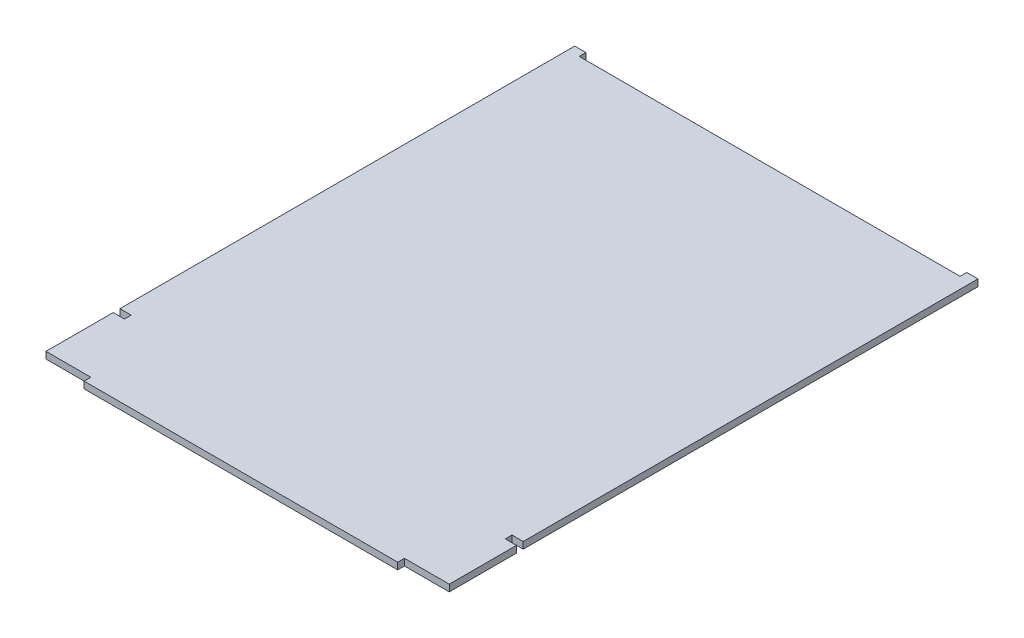
SolidWorks part; units mm, degrees
ref_plane "前视基准面" through (0, 0, 0) normal (0, 0, 1) x (1, 0, 0)
ref_plane "上视基准面" through (0, 0, 0) normal (0, 1, 0) x (1, 0, 0)
ref_plane "右视基准面" through (0, 0, 0) normal (1, 0, 0) x (0, 0, -1)
sketch "草图1" plane through (0, 0, 0) normal (0, 1, 0) x (1, 0, 0)
  line L2 (0, 0) -> (0, 27)
  line L3 (0, 30) -> (5, 30)
  line L4 (180, 0) -> (180, 27)
  line L5 (0, 30) -> (5, 30)
  line L6 (0, 30) -> (0, 230)
  line L7 (5, 230) -> (175, 230)
  line L8 (180, 30) -> (180, 230)
  line L13 (0, 30) -> (5, 30)
  line L14 (5, 30) -> (5, 27)
  line L15 (5, 27) -> (0, 27)
  line L16 (180, 30) -> (175, 30)
  line L17 (175, 30) -> (175, 27)
  line L18 (175, 27) -> (180, 27)
  line L19 (175, 30) -> (180, 30)
  line L20 (175, 30) -> (180, 30)
  line L21 (0, 230) -> (0, 233)
  line L22 (0, 233) -> (5, 233)
  line L23 (5, 233) -> (5, 230)
  line L25 (175, 230) -> (175, 233)
  line L26 (175, 233) -> (180, 233)
  line L27 (180, 233) -> (180, 230)
  line L29 (0, 0) -> (0, -3)
  line L30 (0, -3) -> (20, -3)
  line L31 (20, -3) -> (20, -6)
  line L32 (20, -6) -> (160, -6)
  line L33 (160, -6) -> (160, -3)
  line L34 (160, -3) -> (180, -3)
  line L35 (180, -3) -> (180, 0)
extrude "凸台-拉伸1" add sketch "草图1" along normal blind 3 contours L34 L35 L4 L18 L17 L16 L8 L27 L26 L25 L7 L23 L22 L21 L6 L3 L14 L15 L2 L29 L30 L31 L32 L33
